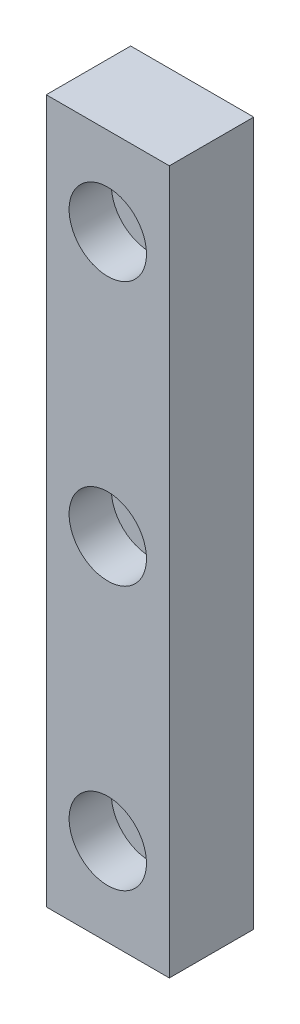
SolidWorks part; units mm, degrees
ref_plane "前视基准面" through (0, 0, 0) normal (0, 0, 1) x (1, 0, 0)
ref_plane "上视基准面" through (0, 0, 0) normal (0, 1, 0) x (1, 0, 0)
ref_plane "右视基准面" through (0, 0, 0) normal (1, 0, 0) x (0, 0, -1)
sketch "草图1" plane through (0, 0, 0) normal (0, 0, 1) x (1, 0, 0)
  line L1 (0, 0) -> (7, 0)
  line L2 (0, 0) -> (0, 40)
  line L3 (0, 40) -> (7, 40)
  line L4 (7, 0) -> (7, 40)
  dimension "D1" = 7
  dimension "D2" = 40
extrude "凸台-拉伸1" add sketch "草图1" along normal blind 4.8
hole_wizard "M2 六角凹头螺钉的柱形沉头孔1" positions "草图2" profile "草图3" counterbore size "M2" standard "ISO"
sketch "草图2" plane through (0, 0, 4.8) normal (0, 0, 1) x (1, 0, 0)
  line L0 (7, 0) -> (7, 40) construction
  line L1 (7, 40) -> (0, 40) construction
  point P2 (3.5, 35)
  point P4 (3.5, 20)
  point P6 (3.5, 5)
  point P9 (0, 0)
  dimension "D1" = 3.5
  dimension "D2" = 5
  dimension "D3" = 15
  dimension "D4" = 15
sketch "草图3" plane through (3.5, 35, 4.8) normal (1, 0, 0) x (0, -1, 0)
  line L0 (0, 0) -> (0, 10.821)
  line L1 (0, 10.821) -> (1.2, 10.1)
  line L2 (1.2, 10.1) -> (1.2, 2.4)
  line L3 (1.2, 2.4) -> (2.2, 2.4)
  line L4 (2.2, 2.4) -> (2.2, 0)
  line L5 (2.2, 0) -> (0, 0)
  line L10 (0, 10.821) -> (-1.2, 10.1) construction
  line L11 (0, -6.35) -> (0, 107.95) construction
  dimension "孔直径" = 2.4
  dimension "孔深度" = 10.1
  dimension "柱形沉头孔直径" = 4.4
  dimension "柱形沉头孔深度" = 2.4
  dimension "导头角度" = 118
